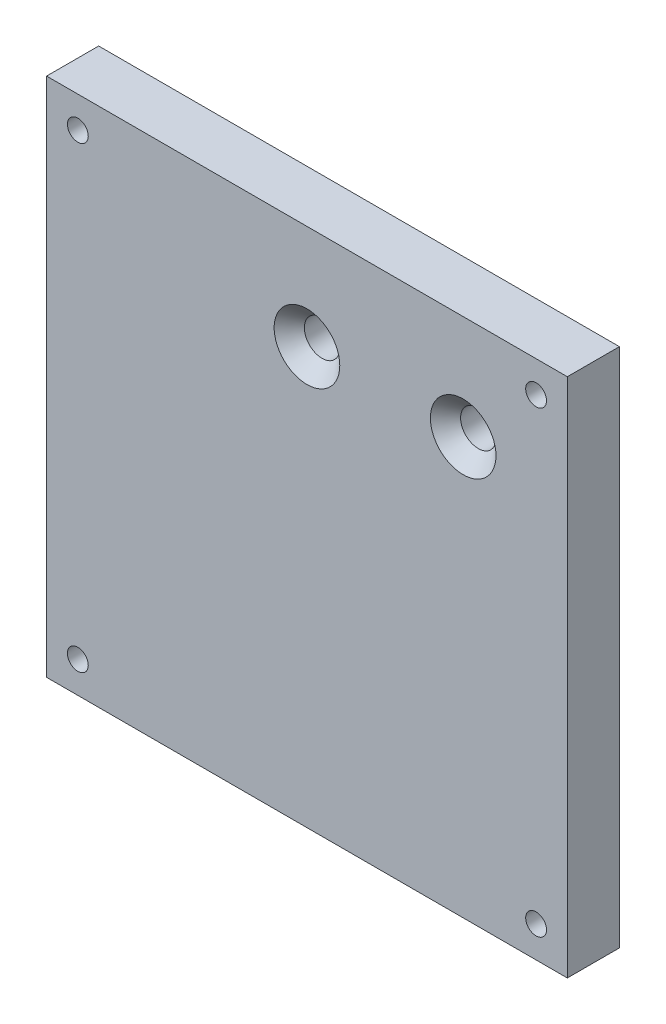
SolidWorks part; units mm, degrees
ref_plane "Plan de face" through (0, 0, 0) normal (0, 0, 1) x (1, 0, 0)
ref_plane "Plan de dessus" through (0, 0, 0) normal (0, 1, 0) x (1, 0, 0)
ref_plane "Plan de droite" through (0, 0, 0) normal (1, 0, 0) x (0, 0, -1)
sketch "Esquisse1" plane through (0, 0, 0) normal (0, 0, 1) x (1, 0, 0)
  line L1 (-38.4431, 48.0825) -> (11.5569, 48.0825)
  line L2 (-38.4431, 48.0825) -> (-38.4431, -1.9175)
  line L3 (-38.4431, -1.9175) -> (11.5569, -1.9175)
  line L4 (11.5569, 48.0825) -> (11.5569, -1.9175)
  circle A2 centre (-35.4431, 45.0825) radius 1
  circle A3 centre (8.5569, 45.0825) radius 1
  circle A4 centre (8.5569, 1.0825) radius 1
  circle A5 centre (-35.4431, 1.0825) radius 1
  point P4 (0, 0)
  point P6 (-11.9306, 45.1292)
  dimension "D2" = 44
  dimension "D8" = 2
  dimension "D3" = 50
  dimension "D4" = 50
  dimension "D5" = 44
  dimension "D9" = 3
  dimension "D10" = 3
  dimension "D11" = 2
  dimension "D12" = 2
extrude "Boss.-Extru.1" add sketch "Esquisse1" along normal blind 5
hole_wizard "Fraisage pour vis à tête fraisée M31" positions "Esquisse3D1" profile "Esquisse3" countersink size "M3" standard "Ansi Metric" end condition through all
sketch3d "Esquisse3D1"
  line L1 (11.5569, -1.9175, 5) -> (11.5569, 48.0825, 5) construction
  line L2 (11.5569, 48.0825, 5) -> (-38.4431, 48.0825, 5) construction
  point P0 (-13.4431, 38.0825, 5)
  point P2 (1.5569, 38.0825, 5)
  point P9 (-69.9328, 61.3931, 0)
  dimension "D1" = 10
  dimension "D2" = 15
  dimension "D3" = 10
  dimension "D4" = 10
sketch "Esquisse3" plane through (-13.4431, 38.0825, 5) normal (1, 0, 0) x (0, -1, 0)
  line L0 (0, 0) -> (0, 5)
  line L1 (0, 5) -> (1.7, 5)
  line L2 (1.7, 5) -> (1.7, 1.45)
  line L3 (1.7, 1.45) -> (3.15, 0)
  line L5 (3.15, 0) -> (0, 0)
  line L6 (-1.7, 1.45) -> (-3.15, 0) construction
  line L11 (0, -6.35) -> (0, 107.95) construction
  dimension "Diamètre du perçage jusqu'au prochain" = 3.4
  dimension "Profondeur du perçage jusqu'au prochain" = 5
  dimension "Diamètre du fraisage entrant" = 6.3
  dimension "Angle du fraisage entrant" = 90
